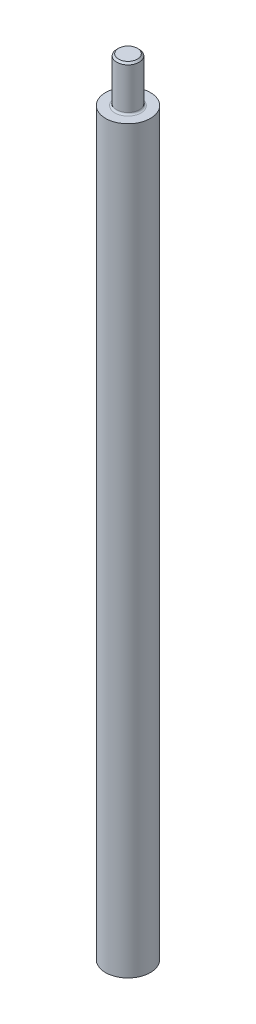
SolidWorks part; units mm, degrees
material "6061-T6 (SS)"
ref_plane "Front Plane" through (0, 0, 0) normal (0, 0, 1) x (1, 0, 0)
ref_plane "Top Plane" through (0, 0, 0) normal (0, 1, 0) x (1, 0, 0)
ref_plane "Right Plane" through (0, 0, 0) normal (1, 0, 0) x (0, 0, -1)
sketch "Sketch1" plane through (0, 0, 0) normal (0, 1, 0) x (1, 0, 0)
  circle A0 centre (0, 0) radius 6.35
  dimension "D1" = 12.7
extrude "Boss-Extrude1" add sketch "Sketch1" along normal mid plane 209.55
sketch "Sketch2" plane through (0, 104.775, 0) normal (0, 1, 0) x (1, 0, 0)
  circle A0 centre (0, 0) radius 3.175
  dimension "D1" = 6.35
extrude "Boss-Extrude2" add sketch "Sketch2" along normal blind 12.7
fillet "Fillet1" radius 0.508 1 edges at (0, 104.775, 3.175)
chamfer "Chamfer1" distance 0.508 angle 45 1 edges at (0, 117.475, 3.175)
